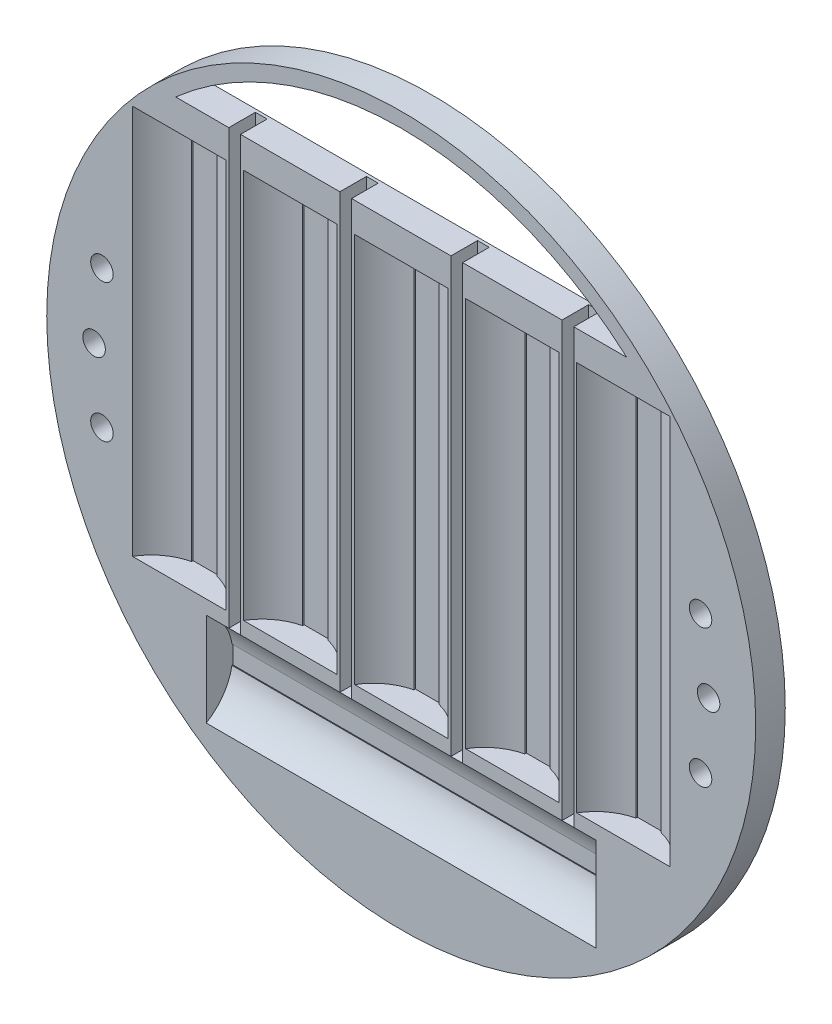
SolidWorks part; units mm, degrees
ref_plane "Front Plane" through (0, 0, 0) normal (0, 0, 1) x (1, 0, 0)
ref_plane "Top Plane" through (0, 0, 0) normal (0, 1, 0) x (1, 0, 0)
ref_plane "Right Plane" through (0, 0, 0) normal (1, 0, 0) x (0, 0, -1)
sketch "Sketch1" plane through (0, 0, 0) normal (0, 0, 1) x (1, 0, 0)
  circle A0 centre (0, 0) radius 60
  dimension "D1" = 120
extrude "Boss-Extrude1" add sketch "Sketch1" along normal blind 5
sketch "Sketch2" plane through (0, 0, 5) normal (0, 0, 1) x (1, 0, 0)
  line L1 (-46, 38) -> (46, 38)
  line L2 (-46, 38) -> (-46, -28)
  line L3 (-46, -28) -> (46, -28)
  line L4 (46, 38) -> (46, -28)
  circle A3 centre (0, 0) radius 60 construction
  point P4 (0, 38)
  dimension "D1" = 92
  dimension "D2" = 66
  dimension "D3" = 38
extrude "Cut-Extrude1" cut sketch "Sketch2" against normal blind 4.5
sketch "Sketch3" plane through (0, 0, 5) normal (0, 0, 1) x (1, 0, 0)
  line L0 (-46, -28) -> (46, -28) construction
  line L1 (-33, -29) -> (33, -29)
  line L2 (-33, -29) -> (-33, -47.4)
  line L3 (-33, -47.4) -> (33, -47.4)
  line L4 (33, -29) -> (33, -47.4)
  point P4 (0, -29)
  dimension "D1" = 66
  dimension "D2" = 18.4
  dimension "D3" = 1
extrude "Cut-Extrude2" cut sketch "Sketch3" against normal blind 4.5
sketch "Sketch4" plane through (0, 0, 0.5) normal (0, 0, 1) x (1, 0, 0)
  line L0 (-38.1739, 43) -> (38.1739, 43)
  line L1 (46, 38) -> (-46, 38) construction
  arc A0 (38.1739, 43) -> (-38.1739, 43) centre (0, 0) ccw
  dimension "D1" = 115
  dimension "D2" = 5
extrude "Cut-Extrude3" cut sketch "Sketch4" against normal through all both and the other way through all
sketch "Sketch8" plane through (-33, 0, 0) normal (1, 0, 0) x (0, 0, -1)
  line L0 (-0.5, -29) -> (-0.5, -47.4) construction
  line L1 (-5, -47.4) -> (-5, -46.1873)
  line L2 (-5, -29) -> (-5, -47.4) construction
  line L3 (-5, -47.4) -> (-0.5, -47.4)
  line L4 (-0.5, -47.4) -> (-0.5, -39.9076)
  line L5 (-5, -29) -> (-5, -30.3695)
  line L6 (-5, -29) -> (-0.5, -29)
  line L7 (-0.5, -29) -> (-5, -29) construction
  line L8 (-0.5, -29) -> (-0.5, -36.7817)
  line L9 (-0.6226, -36.7817) -> (-0.5, -36.7817)
  line L10 (-0.6454, -39.9076) -> (-0.5, -39.9076)
  arc A0 (-5, -46.1873) -> (-0.6454, -39.9076) centre (-9.7, -38.2784) ccw
  arc A1 (-0.6226, -36.7817) -> (-5, -30.3695) centre (-9.7, -38.2784) ccw
  dimension "D1" = 18.4
extrude "Boss-Extrude4" add sketch "Sketch8" along normal up to surface (66 mm away) up to face at (33, -38.2, 2.75)
sketch "Sketch9" plane through (-30.9694, 38, 37.6722) normal (0, -1, 0) x (0, 0, -1)
  line L1 (32.6722, -15.0306) -> (32.6722, -14.5306)
  line L3 (32.6722, -15.0306) -> (37.1722, -15.0306)
  line L4 (37.1722, -15.0306) -> (37.1722, -8.7519)
  line L5 (32.6722, 1.7871) -> (32.6722, 1.2871)
  line L6 (32.6722, 1.7871) -> (37.1722, 1.7871)
  line L7 (37.1722, 76.9694) -> (37.1722, -15.0306) construction
  line L8 (37.1722, 1.7871) -> (37.1722, -4.4916)
  line L9 (36.9222, -4.4916) -> (37.1722, -4.4916)
  line L10 (36.9222, -8.7519) -> (37.1722, -8.7519)
  line L12 (32.6722, 76.9694) -> (32.6722, -15.0306) construction
  line L14 (37.1722, -15.0306) -> (32.6722, -15.0306) construction
  arc A0 (32.6722, -14.5306) -> (36.9222, -8.7519) centre (27.9722, -6.6218) ccw
  arc A1 (36.9222, -4.4916) -> (32.6722, 1.2871) centre (27.9722, -6.6218) ccw
  dimension "D1" = 18.4
  dimension "D2" = 0.5
  dimension "D3" = 0.5
  dimension "D4" = 0.25
  dimension "D5" = 0.25
extrude "Boss-Extrude5" add sketch "Sketch9" along normal up to surface (66 mm away) up to face at (0, -28, 2.75)
pattern_linear "LPattern1" count 5 spacing 18.8 along (1, 0, 0) of "Boss-Extrude5"
sketch "Sketch10" plane through (0, 0, 0) normal (0, 0, -1) x (-1, 0, 0)
  circle A1 centre (-52.0177, 0) radius 1.905
  circle A2 centre (51.9823, 0) radius 1.905
  dimension "D1" = 3.81
  dimension "D2" = 3.81
  dimension "D3" = 52
  dimension "D4" = 52
extrude "Cut-Extrude4" cut sketch "Sketch10" against normal through all
sketch "Sketch11" plane through (0, 0, 5) normal (0, 0, 1) x (1, 0, 0)
  line L1 (-29.1823, 43) -> (-27.2, 43)
  line L2 (-29.1823, 43) -> (-29.1823, -30.3695)
  line L3 (-29.1823, -30.3695) -> (-27.2, -30.3695)
  line L4 (-27.2, 43) -> (-27.2, -30.3695)
  line L5 (-27.2, -28) -> (-27.2, 38) construction
  line L6 (-38.1739, 43) -> (38.1739, 43) construction
  line L7 (33, -30.3695) -> (-33, -30.3695) construction
  line L15 (-29.1823, -28) -> (-29.1823, 38) construction
extrude "Cut-Extrude5" cut sketch "Sketch11" against normal up to surface (4.5 mm away) up to face at (-28.1911, 5, 0.5)
pattern_linear "LPattern2" count 4 spacing 18.8 along (1, 0, 0) of "Cut-Extrude5"
sketch "Sketch12" plane through (0, 0, 0) normal (0, 0, -1) x (-1, 0, 0)
  line L0 (0, 0) -> (0, 34.4289) construction
  circle A1 centre (-50.6546, 11.6736) radius 1.905
  circle A2 centre (-50.6546, -11.6736) radius 1.905
  circle A3 centre (50.6546, -11.6736) radius 1.905
  circle A4 centre (50.6546, 11.6736) radius 1.905
  dimension "D1" = 3.81
  dimension "D2" = 3.81
extrude "Cut-Extrude6" cut sketch "Sketch12" against normal through all
